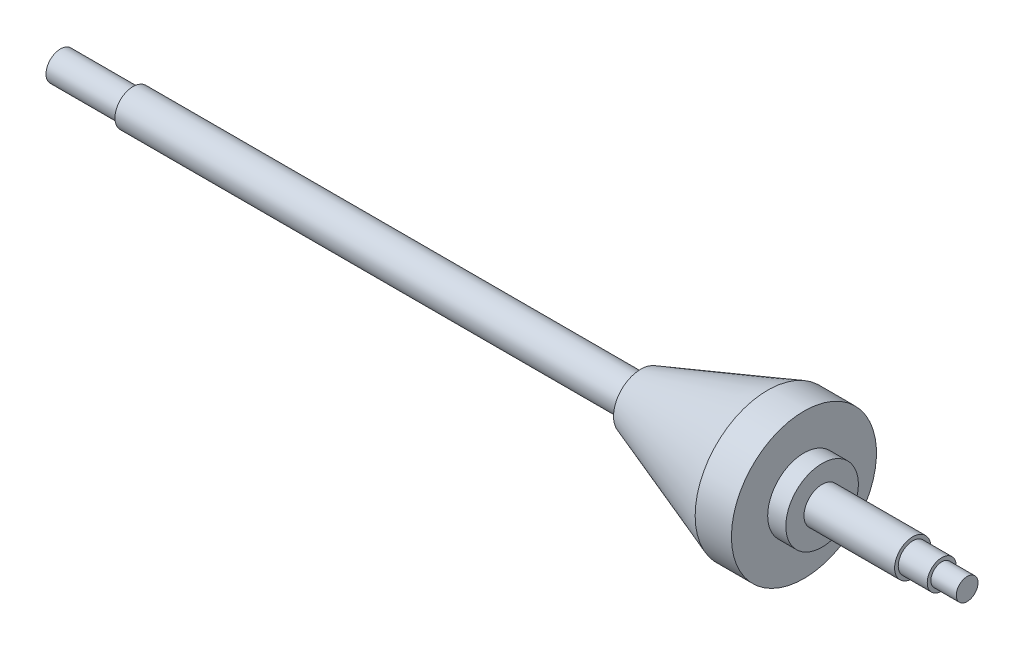
SolidWorks part; units mm, degrees
ref_plane "Front Plane" through (0, 0, 0) normal (0, 0, 1) x (1, 0, 0)
ref_plane "Top Plane" through (0, 0, 0) normal (0, 1, 0) x (1, 0, 0)
ref_plane "Right Plane" through (0, 0, 0) normal (1, 0, 0) x (0, 0, -1)
sketch "Sketch1" plane through (0, 0, 0) normal (0, 0, 1) x (1, 0, 0)
  line L0 (-96.3911, 0) -> (227.5372, 0) construction
  line L1 (-36.2023, 0) -> (-36.2023, 4)
  line L2 (-36.2023, 4) -> (-16.2023, 4)
  line L3 (-16.2023, 4) -> (-16.2023, 5)
  line L4 (123.7977, 5) -> (93.7977, 5)
  line L5 (123.7977, 5) -> (123.7977, 7.5)
  line L6 (123.7977, 7.5) -> (158.7977, 20)
  line L7 (158.7977, 20) -> (168.7977, 20)
  line L8 (168.7977, 20) -> (168.7977, 10)
  line L9 (168.7977, 10) -> (173.7977, 10)
  line L10 (173.7977, 10) -> (173.7977, 5)
  line L11 (173.7977, 5) -> (198.7977, 5)
  line L12 (198.7977, 5) -> (198.7977, 4)
  line L13 (198.7977, 4) -> (206.7977, 4)
  line L14 (206.7977, 4) -> (206.7977, 3)
  line L15 (206.7977, 3) -> (213.7977, 3)
  line L16 (213.7977, 3) -> (213.7977, 0)
  line L17 (93.7977, 5) -> (-16.2023, 5)
  line L18 (-36.2023, 0) -> (213.7977, 0)
  dimension "D1" = 8
  dimension "D2" = 75
  dimension "D3" = 15
  dimension "D4" = 40
  dimension "D5" = 20
  dimension "D6" = 185
  dimension "D7" = 5
  dimension "D8" = 25
  dimension "D9" = 20
  dimension "D10" = 10
  dimension "D11" = 8
  dimension "D12" = 7
  dimension "D13" = 8
  dimension "D14" = 6
  dimension "D15" = 10
  dimension "D16" = 45
revolve "Revolve1" add sketch "Sketch1" angle 360 about L0
